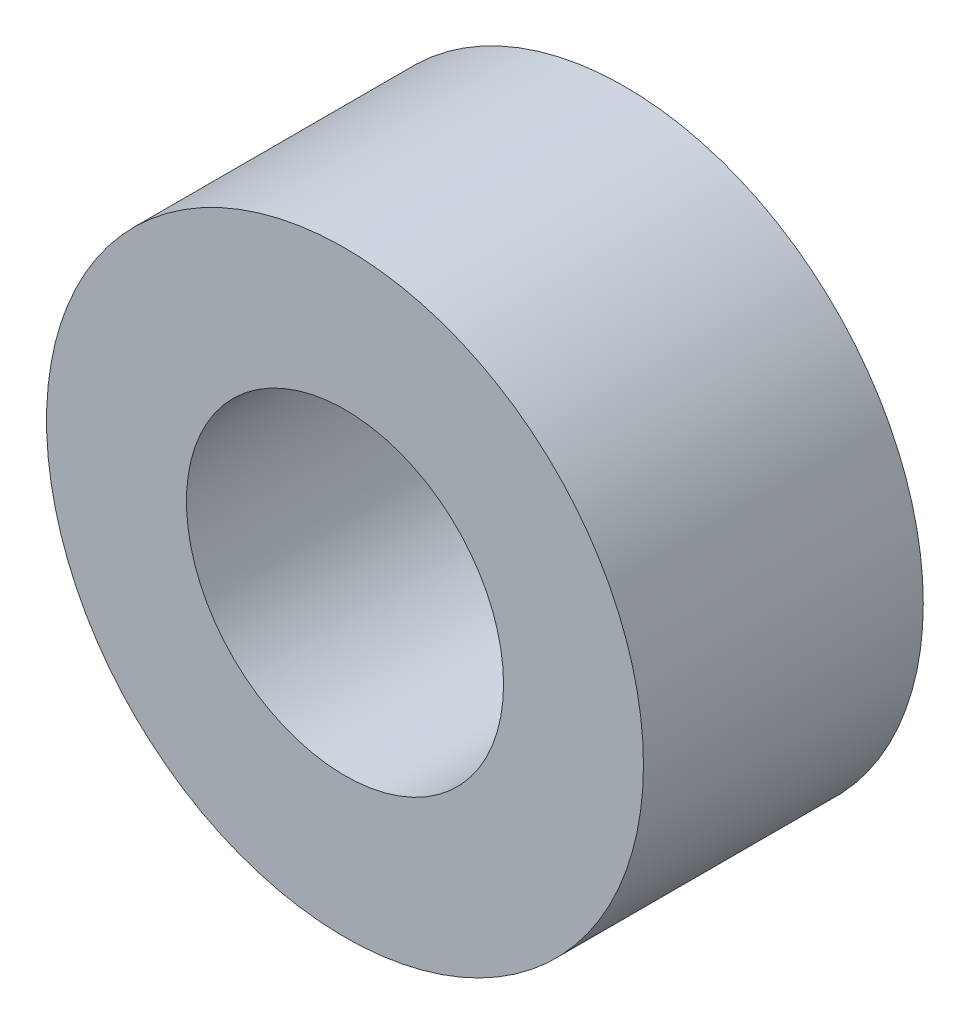
SolidWorks part; units mm, degrees
material "Nylon 101"
ref_plane "Plan de face" through (0, 0, 0) normal (0, 0, 1) x (1, 0, 0)
ref_plane "Plan de dessus" through (0, 0, 0) normal (0, 1, 0) x (1, 0, 0)
ref_plane "Plan de droite" through (0, 0, 0) normal (1, 0, 0) x (0, 0, -1)
sketch "Esquisse1" plane through (0, 0, 0) normal (0, 0, 1) x (1, 0, 0)
  circle A0 centre (-30.3019, 53.6) radius 3.2
  circle A1 centre (-30.3019, 53.6) radius 1.7
  dimension "D1" = 3.4
  dimension "D2" = 1.5
extrude "Boss.-Extru.1" add sketch "Esquisse1" along normal blind 3 contours A0
